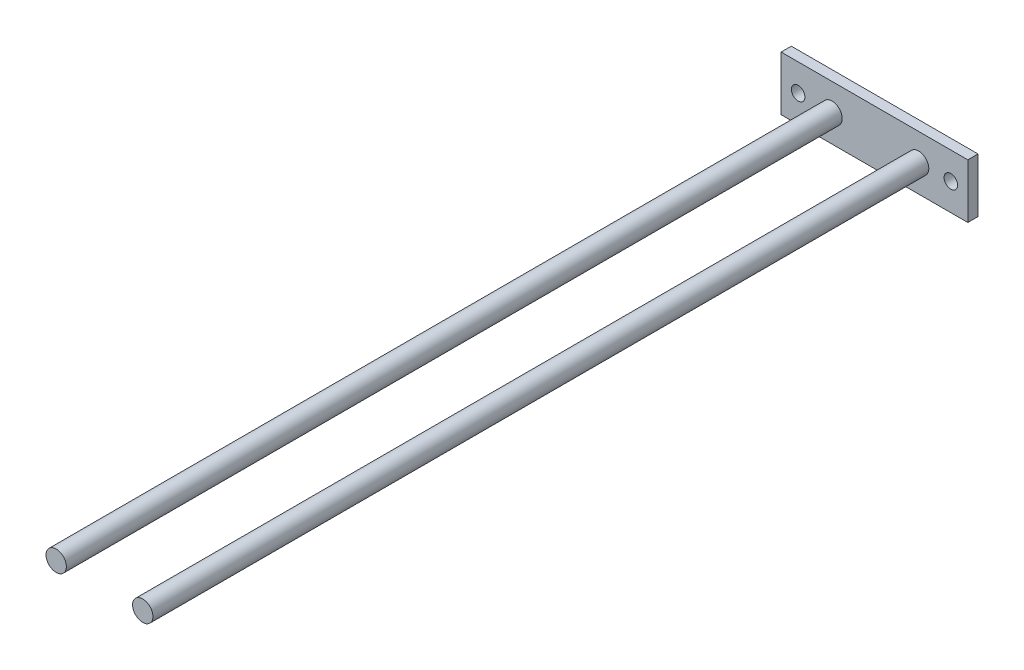
SolidWorks part; units mm, degrees
ref_plane "Front Plane" through (0, 0, 0) normal (0, 0, 1) x (1, 0, 0)
ref_plane "Top Plane" through (0, 0, 0) normal (0, 1, 0) x (1, 0, 0)
ref_plane "Right Plane" through (0, 0, 0) normal (1, 0, 0) x (0, 0, -1)
sketch "Sketch1" plane through (0, 0, 0) normal (0, 0, 1) x (1, 0, 0)
  line L1 (27.5, -8) -> (-27.5, -8)
  line L2 (27.5, -8) -> (27.5, 8)
  line L3 (27.5, 8) -> (-27.5, 8)
  line L4 (-27.5, -8) -> (-27.5, 8)
  line L5 (27.5, -8) -> (-27.5, 8) construction
  line L6 (27.5, 8) -> (-27.5, -8) construction
  circle A0 centre (-22.5, 0) radius 2
  circle A1 centre (22.5, 0) radius 2
  point P0 (0, 0)
  dimension "D3" = 4
  dimension "D1" = 55
  dimension "D2" = 16
  dimension "D4" = 5
  dimension "D5" = 45
extrude "Boss-Extrude1" add sketch "Sketch1" along normal blind 3 contours A1 | A0 | L2 L1 L4 L3
sketch "Sketch3" plane through (0, 0, 3) normal (0, 0, 1) x (1, 0, 0)
  line L0 (-27.5, -8) -> (-27.5, 8) construction
  circle A0 centre (-12.5, 0) radius 3
  circle A1 centre (13, 0) radius 3
  dimension "D3" = 6
  dimension "D4" = 6
  dimension "D1" = 15
  dimension "D2" = 25.5
extrude "Boss-Extrude2" add sketch "Sketch3" along normal blind 228.6
